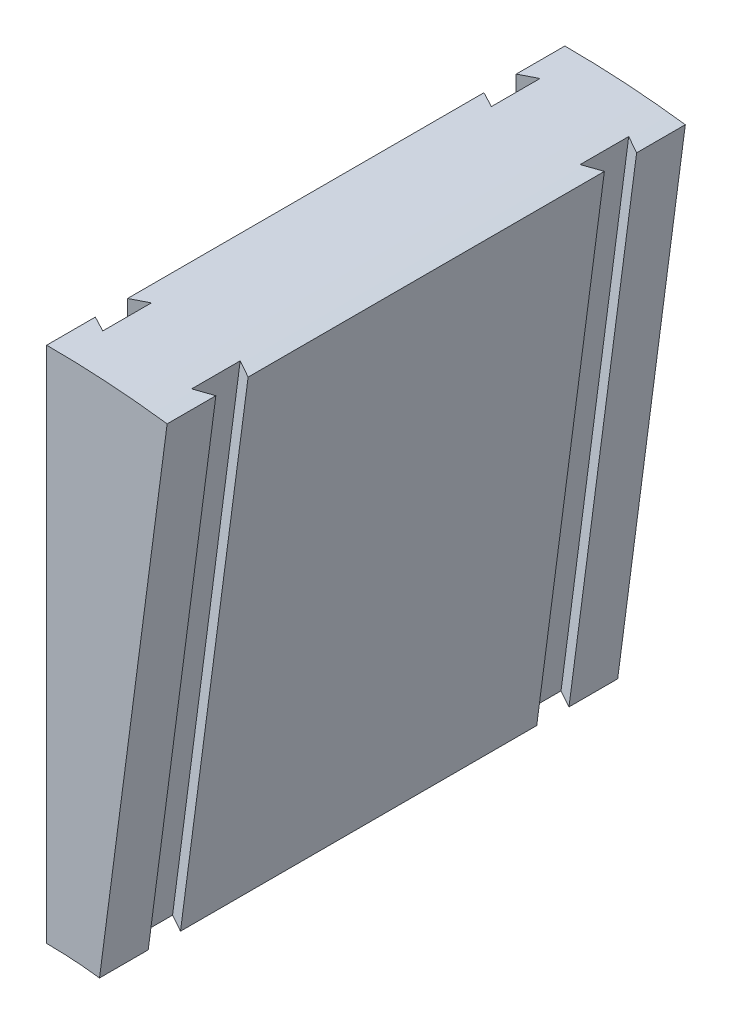
SolidWorks part; units mm, degrees
ref_plane "Front Plane" through (0, 0, 0) normal (0, 0, 1) x (1, 0, 0)
ref_plane "Top Plane" through (0, 0, 0) normal (0, 1, 0) x (1, 0, 0)
ref_plane "Right Plane" through (0, 0, 0) normal (1, 0, 0) x (0, 0, -1)
sketch "Sketch1" plane through (0, 0, 0) normal (0, 0, 1) x (1, 0, 0)
  line L0 (0, 0) -> (0, 180.975) construction
  line L2 (0, 0) -> (156.7289, 90.4875) construction
  line L4 (0, 79.375) -> (0, 180.975)
  line L6 (23.622, 179.4267) -> (10.3605, 78.6959)
  circle A10 centre (0, 0) radius 79.375 construction
  circle A11 centre (0, 0) radius 180.975 construction
  arc A12 (0, 180.975) -> (23.622, 179.4267) centre (0, 0) cw
  arc A13 (0, 79.375) -> (10.3605, 78.6959) centre (0, 0) cw
  dimension "D1" = 158.75
  dimension "D3" = 60
  dimension "D2" = 101.6
  dimension "D4" = 7.5
extrude "Boss-Extrude1" add sketch "Sketch1" along normal blind 101.6
ref_plane "Plane1" through (10.3605, 78.6959, 0) normal (-0.1305, -0.9914, 0) x (0, 0, -1)
ref_plane "Plane2" through (0, 79.375, 0) normal (0, -1, 0) x (0, 0, -1)
sketch "Sketch5" plane through (10.3605, 78.6959, 0) normal (-0.1305, -0.9914, 0) x (0, 0, -1)
  line L1 (-101.6, 0) -> (0, 0) construction
  line L4 (-93.6499, -3.175) -> (-84.1249, -3.175)
  line L8 (-85.725, 0) -> (-92.0498, 0)
  line L9 (-50.8, 0) -> (-50.8, 24.8181) construction
  line L20 (-93.6499, -3.175) -> (-92.0498, 0)
  line L21 (-85.725, 0) -> (-84.1249, -3.175)
  line L22 (-15.875, 0) -> (-17.4751, -3.175)
  line L23 (-7.9501, -3.175) -> (-9.5502, 0)
  line L24 (-15.875, 0) -> (-9.5502, 0)
  line L25 (-7.9501, -3.175) -> (-17.4751, -3.175)
  point P4 (-88.8874, 0)
  dimension "D1" = 9.525
  dimension "D2" = 6.3248
  dimension "D3" = 3.175
  dimension "D5" = 12.7126
extrude "Cut-Extrude1" cut sketch "Sketch5" against normal through all both and the other way through all
sketch "Sketch6" plane through (0, 79.375, 0) normal (0, -1, 0) x (0, 0, -1)
  line L1 (-101.6, 0) -> (0, 0) construction
  line L4 (-84.1375, 3.0599) -> (-93.6625, 3.0599)
  line L8 (-92.0624, 0) -> (-85.7376, 0)
  line L10 (-92.0498, 10.3605) -> (-85.725, 10.3605) construction
  line L13 (-93.6625, 3.0599) -> (-92.0624, 0)
  line L14 (-85.7376, 0) -> (-84.1375, 3.0599)
  line L15 (-50.8, 0) -> (-50.8, 34.8679) construction
  line L16 (-15.8624, 0) -> (-17.4625, 3.0599)
  line L17 (-7.9375, 3.0599) -> (-9.5376, 0)
  line L26 (-84.1249, 7.2044) -> (-93.6499, 7.2044) construction
  line L27 (-9.5376, 0) -> (-15.8624, 0)
  line L28 (-17.4625, 3.0599) -> (-7.9375, 3.0599)
  point P9 (0, 0)
  point P11 (0, 0)
  point P16 (-91.3332, 10.343)
  point P17 (-86.8643, 10.3605)
  point P18 (-88.9, 0)
  point P20 (0, 0)
  point P23 (0, 0)
  dimension "D1" = 12.7
  dimension "D2" = 3.0599
extrude "Cut-Extrude2" cut sketch "Sketch6" against normal through all both and the other way through all
